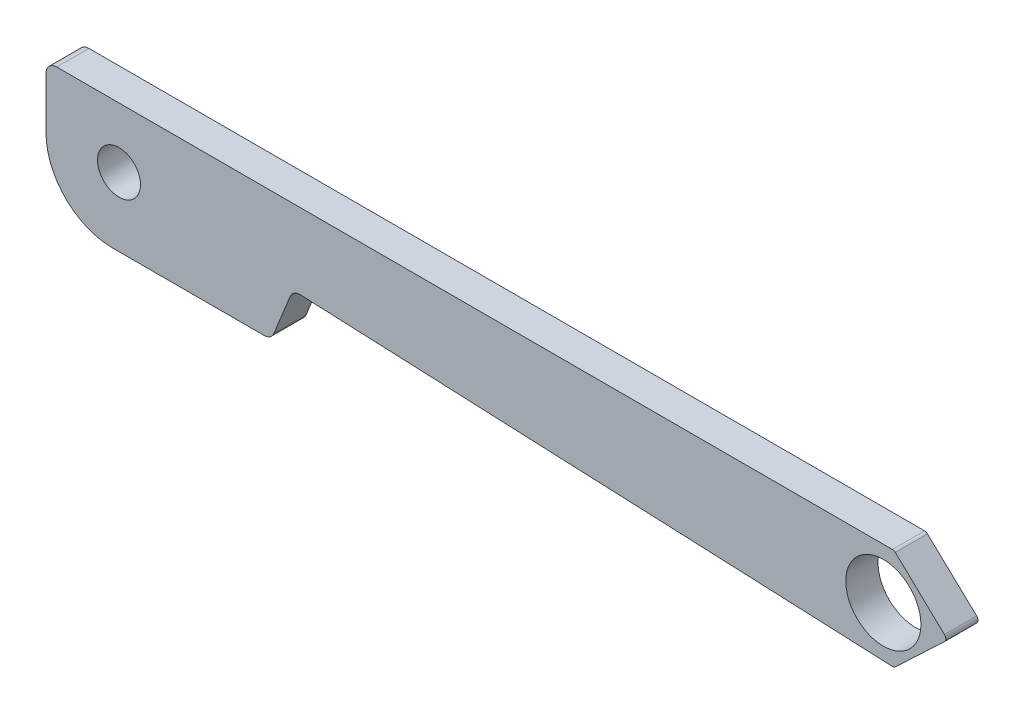
SolidWorks part; units mm, degrees
material "1060 Alloy"
ref_plane "Front Plane" through (0, 0, 0) normal (0, 0, 1) x (1, 0, 0)
ref_plane "Top Plane" through (0, 0, 0) normal (0, 1, 0) x (1, 0, 0)
ref_plane "Right Plane" through (0, 0, 0) normal (1, 0, 0) x (0, 0, -1)
sketch "Sketch1" plane through (0, 0, 0) normal (0, 0, 1) x (1, 0, 0)
  line L7 (0, 0) -> (0, 6)
  line L8 (0, 6) -> (39.5, 6)
  line L9 (39.5, 6) -> (42, 3.6387)
  line L10 (42, 3.6387) -> (39.5, 1.2775)
  line L11 (39.5, 1.2775) -> (11.5, 2.5)
  line L12 (11.5, 2.5) -> (10.4899, 0)
  line L13 (10.4899, 0) -> (0, 0)
  circle A0 centre (39, 3.6387) radius 1.75
  dimension "D10" = 3.5
  dimension "D1" = 6
  dimension "D2" = 42
  dimension "D3" = 2.5
  dimension "D4" = 2.5
  dimension "D5" = 39.5
  dimension "D6" = 11.5
  dimension "D7" = 2.5
  dimension "D8" = 112
  dimension "D9" = 0.5
extrude "Boss-Extrude1" add sketch "Sketch1" along normal blind 1.5
fillet "Fillet1" radius 0.5 3 edges at (0, 6, 0.75) (10.4899, 0, 0.75) (11.5, 2.5, 0.75)
fillet "Fillet2" radius 0.2 3 edges at (39.5, 1.2775, 0.75) (42, 3.6387, 0.75) (39.5, 6, 0.75)
sketch "Sketch5" plane through (0, 0, 1.5) normal (0, 0, 1) x (1, 0, 0)
  line L2 (0, 0) -> (10.1527, 0) construction
  line L3 (0, 5.5) -> (0, 0) construction
  circle A0 centre (3.4, 3.2) radius 1
  dimension "D1" = 2
  dimension "D2" = 3.2
  dimension "D3" = 3.4
extrude "Cut-Extrude3" cut sketch "Sketch5" against normal through all
fillet "Fillet3" radius 3.1 1 edges at (0, 0, 0.75)
